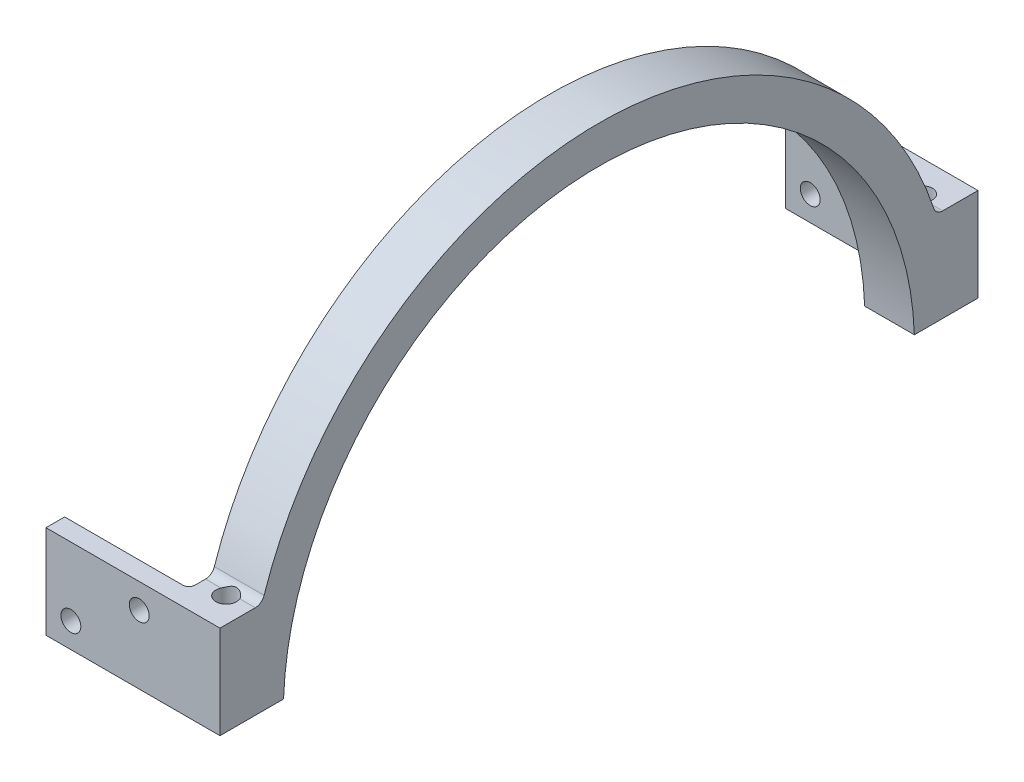
SolidWorks part; units mm, degrees
material "1060 Alloy"
ref_plane "Front Plane" through (0, 0, 0) normal (0, 0, 1) x (1, 0, 0)
ref_plane "Top Plane" through (0, 0, 0) normal (0, 1, 0) x (1, 0, 0)
ref_plane "Right Plane" through (0, 0, 0) normal (1, 0, 0) x (0, 0, -1)
sketch "Sketch1" plane through (0, 0, 0) normal (1, 0, 0) x (0, 0, -1)
  line L2 (-60.9955, 1.9) -> (-50.7645, 1.9)
  line L3 (50.7645, 1.9) -> (61.0045, 1.9)
  line L4 (-60.9955, 1.9) -> (-60.9955, 16.9)
  line L5 (-60.9955, 16.9) -> (-55.3202, 16.9)
  line L6 (61.0045, 1.9) -> (61.0045, 16.9)
  line L7 (61.0045, 16.9) -> (55.3202, 16.9)
  arc A0 (50.7645, 1.9) -> (-50.7645, 1.9) centre (0, 0) ccw
  arc A1 (53.8969, 17.9266) -> (-53.8969, 17.9266) centre (0, 0) ccw
  circle A2 centre (0, 0) radius 56.8 construction
  circle A3 centre (0, 0) radius 50.8 construction
  arc A5 (55.3202, 16.9) -> (53.8969, 17.9266) centre (55.3202, 18.4) cw
  arc A7 (-55.3202, 16.9) -> (-53.8969, 17.9266) centre (-55.3202, 18.4) ccw
  dimension "D1" = 101.6
  dimension "D2" = 122
  dimension "D3" = 15
  dimension "D6" = 10.24
  dimension "D4" = 15
  dimension "D7" = 1.9
  dimension "D8" = 1.9
  dimension "D5" = 6
extrude "Boss-Extrude1" add sketch "Sketch1" along normal blind 8
hole_wizard "M4 Tapped Hole1" positions "Sketch5" profile "Sketch4" tap size "M4" standard "ISO" end condition through all
sketch "Sketch5" plane through (0, 1.9, 0) normal (0, 1, 0) x (1, 0, 0)
  line L0 (8, 61.0045) -> (8, 55.3202) construction
  line L1 (8, -60.9955) -> (0, -60.9955) construction
  line L2 (8, 61.0045) -> (0, 61.0045) construction
  line L4 (8, -55.3202) -> (8, -60.9955) construction
  point P0 (4, 56.0045)
  point P11 (4, -55.9955)
  dimension "D1" = 4
  dimension "D2" = 5
  dimension "D3" = 5
  dimension "D4" = 4
sketch "Sketch4" plane through (4, 1.9, -56.0045) normal (1, 0, 0) x (0, 0, -1)
  line L0 (0, 0) -> (0, 54.9)
  line L1 (0, 54.9) -> (1.65, 54.9)
  line L2 (1.65, 54.9) -> (1.65, 0)
  line L5 (1.65, 0) -> (0, 0)
  line L11 (0, -6.35) -> (0, 107.95) construction
  dimension "Thru Tap Drill Dia." = 3.3
  dimension "Thru Tap Drill Depth" = 54.9
cosmetic thread "Hole Thread3" parameters "D2"=4
cosmetic thread "Hole Thread4" parameters "D2"=4
ref_plane "Plane1" through (0, 0, -0.0045) normal (0, 0, -1) x (-1, 0, 0)
sketch "Sketch8" plane through (0, 0, 60.9955) normal (0, 0, 1) x (1, 0, 0)
  line L1 (0, 1.9) -> (-20, 1.9)
  line L2 (0, 1.9) -> (0, 16.9)
  line L3 (0, 16.9) -> (-20, 16.9)
  line L4 (-20, 1.9) -> (-20, 16.9)
  dimension "D1" = 20
extrude "Boss-Extrude2" add sketch "Sketch8" against normal blind 3
fillet "Fillet1" radius 1 1 edges
hole_wizard "M3 Clearance Hole1" positions "Sketch10" profile "Sketch9" hole size "M3" standard "ISO"
sketch "Sketch10" plane through (0, 0, 57.9955) normal (0, 0, -1) x (-1, 0, 0)
  line L4 (1, 16.9) -> (1, 1.9) construction
  line L5 (20, 16.9) -> (20, 1.9) construction
  line L6 (1, 16.9) -> (20, 16.9) construction
  line L7 (20, 1.9) -> (1, 1.9) construction
  point P0 (5, 12.9)
  point P21 (16, 5.9)
  dimension "D1" = 4
  dimension "D2" = 4
  dimension "D3" = 4
  dimension "D4" = 4
sketch "Sketch9" plane through (-5, 12.9, 57.9955) normal (1, 0, 0) x (0, 1, 0)
  line L0 (0, 0) -> (0, 15.9614)
  line L1 (0, 15.9614) -> (1.6, 15)
  line L2 (1.6, 15) -> (1.6, 0)
  line L5 (1.6, 0) -> (0, 0)
  line L10 (0, 15.9614) -> (-1.6, 15) construction
  line L11 (0, -6.35) -> (0, 107.95) construction
  dimension "Hole Dia." = 3.2
  dimension "Hole Depth" = 15
  dimension "Drill Angle" = 118
mirror "Mirror1" about plane through (0, 0, -0.0045) normal (0, 0, -1) of "M3 Clearance Hole1", "Fillet1", "Boss-Extrude2"
